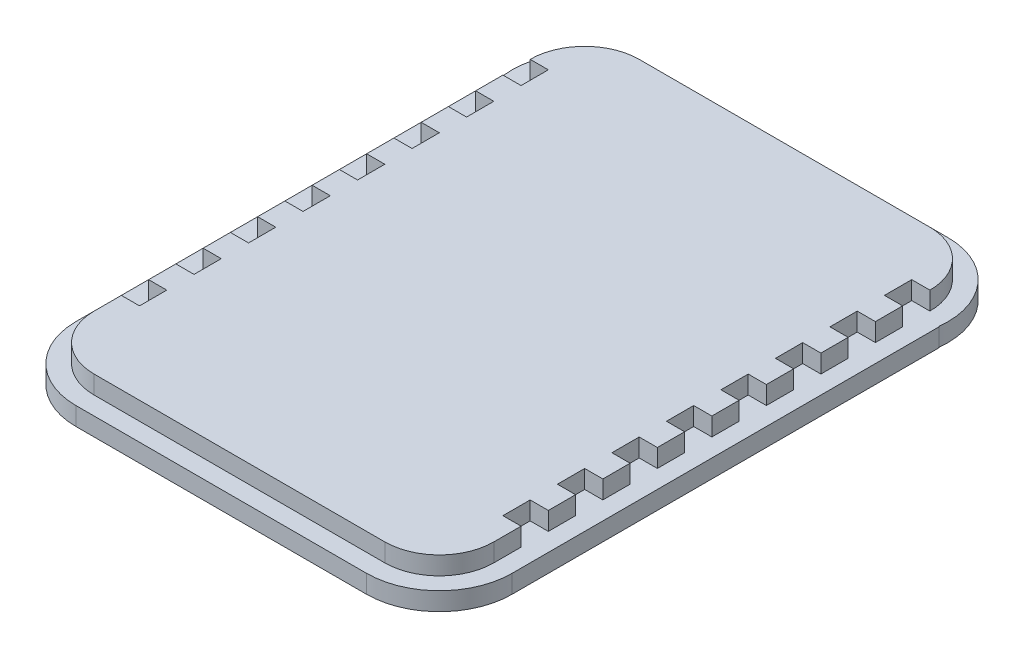
SolidWorks part; units mm, degrees
ref_plane "Front Plane" through (0, 0, 0) normal (0, 0, 1) x (1, 0, 0)
ref_plane "Top Plane" through (0, 0, 0) normal (0, 1, 0) x (1, 0, 0)
ref_plane "Right Plane" through (0, 0, 0) normal (1, 0, 0) x (0, 0, -1)
sketch "Sketch1" plane through (0, 0, 0) normal (0, 1, 0) x (1, 0, 0)
  line L0 (144.3558, 286.3848) -> (805.6847, 286.3848) construction
  line L2 (0, 0) -> (220, 0)
  line L3 (0, 0) -> (0, 300)
  line L4 (0, 300) -> (220, 300)
  line L5 (220, 0) -> (220, 300)
  dimension "D1" = 220
  dimension "D2" = 300
extrude "Boss-Extrude1" add sketch "Sketch1" along normal blind 10
fillet "Fillet1" radius 30 4 edges at (0, 5, 0) (220, 5, 0) (220, 5, -300) (0, 5, -300)
sketch "Sketch8" plane through (0, 0, 0) normal (-1, 0, 0) x (0, 0, 1)
  line L0 (-270, 0) -> (-30, 0) construction
  line L1 (-270, 0) -> (-255, 0)
  line L2 (-270, 0) -> (-270, 10)
  line L3 (-270, 10) -> (-255, 10)
  line L4 (-255, 0) -> (-255, 10)
  line L5 (-270, 10) -> (-270, 0) construction
  line L6 (-270, 10) -> (-30, 10) construction
  line L7 (-255, 0) -> (-255, 10)
  line L8 (-255, 0) -> (-240, 0)
  line L9 (-240, 0) -> (-240, 10)
  line L10 (-255, 10) -> (-240, 10)
  line L11 (-240, 0) -> (-240, 10)
  line L12 (-240, 0) -> (-225, 0)
  line L13 (-225, 0) -> (-225, 10)
  line L14 (-240, 10) -> (-225, 10)
  line L15 (-225, 0) -> (-225, 10)
  line L16 (-225, 0) -> (-210, 0)
  line L17 (-210, 0) -> (-210, 10)
  line L18 (-225, 10) -> (-210, 10)
  line L19 (-210, 0) -> (-210, 10)
  line L20 (-210, 0) -> (-195, 0)
  line L21 (-195, 0) -> (-195, 10)
  line L22 (-210, 10) -> (-195, 10)
  line L23 (-195, 0) -> (-195, 10)
  line L24 (-195, 0) -> (-180, 0)
  line L25 (-180, 0) -> (-180, 10)
  line L26 (-195, 10) -> (-180, 10)
  line L27 (-180, 0) -> (-180, 10)
  line L28 (-180, 0) -> (-165, 0)
  line L29 (-165, 0) -> (-165, 10)
  line L30 (-180, 10) -> (-165, 10)
  line L31 (-165, 0) -> (-165, 10)
  line L32 (-165, 0) -> (-150, 0)
  line L33 (-150, 0) -> (-150, 10)
  line L34 (-165, 10) -> (-150, 10)
  line L35 (-150, 0) -> (-150, 10)
  line L36 (-150, 0) -> (-135, 0)
  line L37 (-135, 0) -> (-135, 10)
  line L38 (-150, 10) -> (-135, 10)
  line L39 (-135, 0) -> (-135, 10)
  line L40 (-135, 0) -> (-120, 0)
  line L41 (-120, 0) -> (-120, 10)
  line L42 (-135, 10) -> (-120, 10)
  line L43 (-120, 0) -> (-120, 10)
  line L44 (-120, 0) -> (-105, 0)
  line L45 (-105, 0) -> (-105, 10)
  line L46 (-120, 10) -> (-105, 10)
  line L47 (-105, 0) -> (-105, 10)
  line L48 (-105, 0) -> (-90, 0)
  line L49 (-90, 0) -> (-90, 10)
  line L50 (-105, 10) -> (-90, 10)
  line L51 (-90, 0) -> (-90, 10)
  line L52 (-90, 0) -> (-75, 0)
  line L53 (-75, 0) -> (-75, 10)
  line L54 (-90, 10) -> (-75, 10)
  line L55 (-75, 0) -> (-75, 10)
  line L56 (-75, 0) -> (-60, 0)
  line L57 (-60, 0) -> (-60, 10)
  line L58 (-75, 10) -> (-60, 10)
  line L59 (-60, 0) -> (-60, 10)
  line L60 (-60, 0) -> (-45, 0)
  line L61 (-45, 0) -> (-45, 10)
  line L62 (-60, 10) -> (-45, 10)
  line L63 (-45, 0) -> (-45, 10)
  line L64 (-45, 0) -> (-30, 0)
  line L65 (-30, 0) -> (-30, 10)
  line L66 (-45, 10) -> (-30, 10)
  line M5 (-270, 0) -> (-30, 0)
  line M7 (-30, 10) -> (-270, 10)
  line M8 (-270, 10) -> (-270, 0)
  dimension "D1" = 15
  dimension "D2" = 16
sketch "Sketch9" plane through (220, 0, 0) normal (1, 0, 0) x (0, 0, -1)
  line L0 (30, 0) -> (270, 0) construction
  line L1 (30, 10) -> (45, 10)
  line L2 (30, 10) -> (30, 0)
  line L3 (30, 0) -> (45, 0)
  line L4 (45, 10) -> (45, 0)
  line L5 (45, 10) -> (45, 0)
  line L6 (45, 10) -> (60, 10)
  line L7 (60, 10) -> (60, 0)
  line L8 (45, 0) -> (60, 0)
  line L9 (60, 10) -> (60, 0)
  line L10 (60, 10) -> (75, 10)
  line L11 (75, 10) -> (75, 0)
  line L12 (60, 0) -> (75, 0)
  line L13 (75, 10) -> (75, 0)
  line L14 (75, 10) -> (90, 10)
  line L15 (90, 10) -> (90, 0)
  line L16 (75, 0) -> (90, 0)
  line L17 (90, 10) -> (90, 0)
  line L18 (90, 10) -> (105, 10)
  line L19 (105, 10) -> (105, 0)
  line L20 (90, 0) -> (105, 0)
  line L21 (105, 10) -> (105, 0)
  line L22 (105, 10) -> (120, 10)
  line L23 (120, 10) -> (120, 0)
  line L24 (105, 0) -> (120, 0)
  line L25 (120, 10) -> (120, 0)
  line L26 (120, 10) -> (135, 10)
  line L27 (135, 10) -> (135, 0)
  line L28 (120, 0) -> (135, 0)
  line L29 (135, 10) -> (135, 0)
  line L30 (135, 10) -> (150, 10)
  line L31 (150, 10) -> (150, 0)
  line L32 (135, 0) -> (150, 0)
  line L33 (150, 10) -> (150, 0)
  line L34 (150, 10) -> (165, 10)
  line L35 (165, 10) -> (165, 0)
  line L36 (150, 0) -> (165, 0)
  line L37 (165, 10) -> (165, 0)
  line L38 (165, 10) -> (180, 10)
  line L39 (180, 10) -> (180, 0)
  line L40 (165, 0) -> (180, 0)
  line L41 (180, 10) -> (180, 0)
  line L42 (180, 10) -> (195, 10)
  line L43 (195, 10) -> (195, 0)
  line L44 (180, 0) -> (195, 0)
  line L45 (195, 10) -> (195, 0)
  line L46 (195, 10) -> (210, 10)
  line L47 (210, 10) -> (210, 0)
  line L48 (195, 0) -> (210, 0)
  line L49 (210, 10) -> (210, 0)
  line L50 (210, 10) -> (225, 10)
  line L51 (225, 10) -> (225, 0)
  line L52 (210, 0) -> (225, 0)
  line L53 (225, 10) -> (225, 0)
  line L54 (225, 10) -> (240, 10)
  line L55 (240, 10) -> (240, 0)
  line L56 (225, 0) -> (240, 0)
  line L57 (240, 10) -> (240, 0)
  line L58 (240, 10) -> (255, 10)
  line L59 (255, 10) -> (255, 0)
  line L60 (240, 0) -> (255, 0)
  line L61 (255, 10) -> (255, 0)
  line L62 (255, 10) -> (270, 10)
  line L63 (270, 10) -> (270, 0)
  line L64 (255, 0) -> (270, 0)
  line L65 (30, 10) -> (45, 10) construction
  line M9 (270, 10) -> (30, 10)
  line M11 (30, 0) -> (270, 0)
  line M12 (270, 0) -> (270, 10)
  dimension "D1" = 15
  dimension "D3" = 15
  dimension "D2" = 16
extrude "Cut-Extrude1" cut sketch "Sketch9" against normal blind 10 contours L59 M9 M11 M12 | L55 L51 M9 M11 | L47 L43 M9 M11 | L39 L35 M9 M11 | L31 L27 M9 M11 | L23 L19 M9 M11 | L15 L11 M9 M11 | L7 L4 M9 M11
extrude "Cut-Extrude2" cut sketch "Sketch8" against normal blind 10 contours L4 M5 M7 M8 | L13 L9 M5 M7 | L21 L17 M5 M7 | L29 L25 M5 M7 | L37 L33 M5 M7 | L45 L41 M5 M7 | L53 L49 M5 M7 | L61 L57 M5 M7
sketch "Sketch11" plane through (0, 0, 0) normal (0, -1, 0) x (1, 0, 0)
  line L40 (230, -265) -> (230, -30)
  line L44 (229.6863, -265) -> (230, -265)
  line L48 (229.6863, -265) -> (230, -265)
  line L62 (230, -265) -> (230, -30)
  line L71 (-10, -30) -> (-10, -265)
  line L73 (-10, -30) -> (-10, -265)
  line L132 (30, -310) -> (190, -310)
  line L135 (190, 10) -> (30, 10)
  line L137 (-10, -265) -> (-9.6863, -265)
  line L138 (30, -310) -> (190, -310)
  line L141 (190, 10) -> (30, 10)
  line L143 (-10, -265) -> (-9.6863, -265)
  arc A8 (-9.6863, -265) -> (30, -310) centre (30, -270) ccw
  arc A9 (190, -310) -> (229.6863, -265) centre (190, -270) ccw
  arc A10 (230, -30) -> (190, 10) centre (190, -30) ccw
  arc A11 (30, 10) -> (-10, -30) centre (30, -30) ccw
  arc A12 (-9.6863, -265) -> (30, -310) centre (30, -270) ccw
  arc A13 (190, -310) -> (229.6863, -265) centre (190, -270) ccw
  arc A14 (230, -30) -> (190, 10) centre (190, -30) ccw
  arc A15 (30, 10) -> (-10, -30) centre (30, -30) ccw
  dimension "D1" = 10
extrude "Boss-Extrude3" add sketch "Sketch11" along normal blind 10
